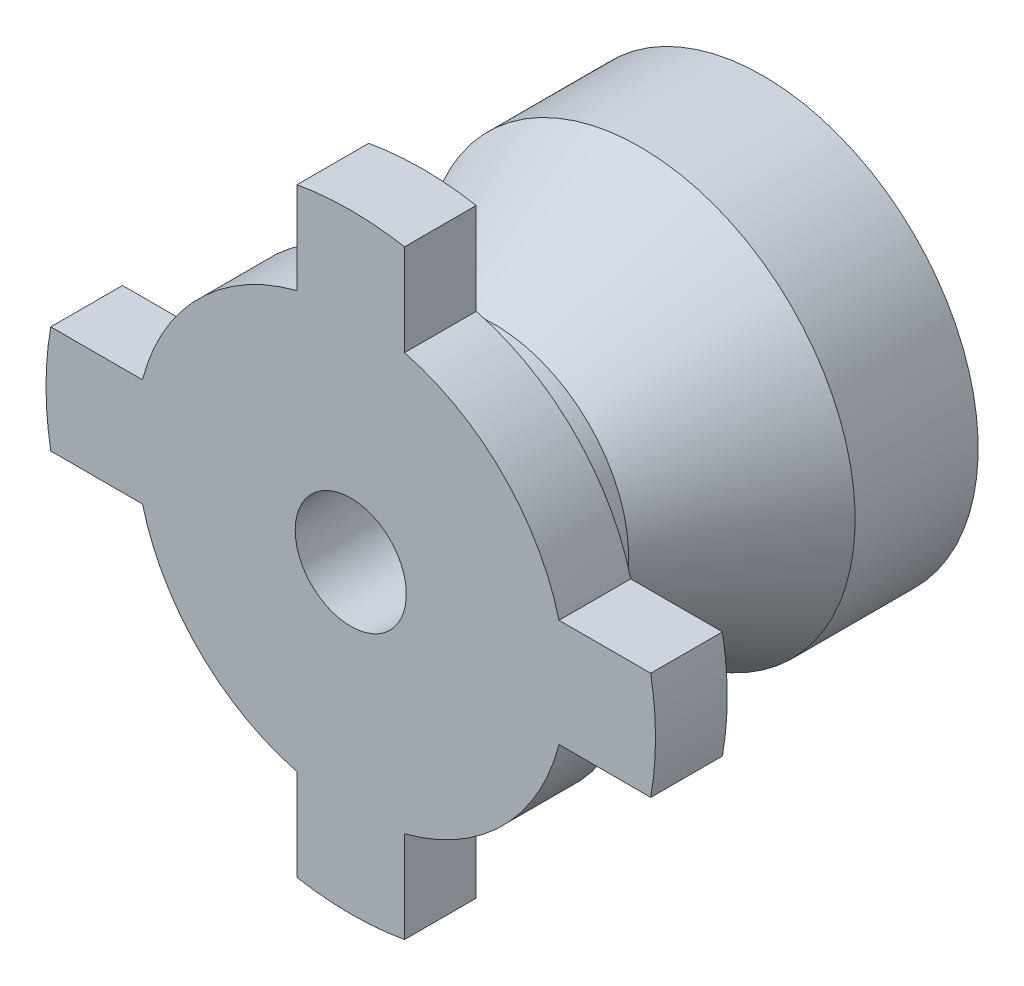
SolidWorks part; units mm, degrees
ref_plane "Front Plane" through (0, 0, 0) normal (0, 0, 1) x (1, 0, 0)
ref_plane "Top Plane" through (0, 0, 0) normal (0, 1, 0) x (1, 0, 0)
ref_plane "Right Plane" through (0, 0, 0) normal (1, 0, 0) x (0, 0, -1)
sketch "Sketch1" plane through (0, 0, 0) normal (0, 1, 0) x (1, 0, 0)
  line L0 (-20.9062, 0) -> (-6, 0) construction
  line L1 (0, 14.2603) -> (0, -16.1973) construction
  line L2 (-1.55, 0) -> (-6, 0)
  line L3 (0, 0) -> (23.1772, 0) construction
  line L4 (-6, 0) -> (-6, 2)
  line L5 (-6, 2) -> (-3.75, 2)
  line L6 (-3.75, 2) -> (-3.75, 4)
  line L7 (-3.75, 4) -> (-6, 8.0672)
  line L8 (-6, 8.0672) -> (-6, 11.5)
  line L9 (-6, 11.5) -> (-5, 11.5)
  line L10 (-5, 11.5) -> (-5, 9)
  line L11 (-5, 9) -> (-2.6884, 9)
  line L12 (-2.6884, 9) -> (-2.6884, 7.5)
  line L13 (-2.6884, 7.5) -> (-1.55, 7.5)
  line L14 (-1.55, 7.5) -> (-1.55, 0)
  point P7 (-1.55, 0)
  point P9 (-3.75, 0)
  point P10 (0, 11.5)
  dimension "D1" = 6
  dimension "D2" = 1.55
  dimension "D3" = 3.75
  dimension "D4" = 2
  dimension "D5" = 11.5
  dimension "D6" = 4
  dimension "D7" = 1.5
  dimension "D8" = 5
  dimension "D9" = 6
  dimension "D10" = 2.5
revolve "Revolve1" add sketch "Sketch1" angle 360 about L1
sketch "Sketch2" plane through (0, 0, 0) normal (0, 0, 1) x (1, 0, 0)
  line L0 (0, 9.4104) -> (0, -10.1354) construction
  line L1 (-13.1705, 0) -> (10.5119, 0) construction
  line L3 (-8.3666, 1.5) -> (-5.8095, 1.5)
  line L4 (-8.3666, -1.5) -> (-5.8095, -1.5)
  line L5 (1.5, 8.3666) -> (1.5, 5.8095)
  line L6 (-1.5, 8.3666) -> (-1.5, 5.8095)
  line L8 (8.3666, -1.5) -> (5.8095, -1.5)
  line L9 (8.3666, 1.5) -> (5.8095, 1.5)
  line L11 (-1.5, -8.3666) -> (-1.5, -5.8095)
  line L12 (1.5, -8.3666) -> (1.5, -5.8095)
  arc A0 (-5.8095, 1.5) -> (-5.8095, -1.5) centre (0, 0) ccw
  arc A1 (1.5, 5.8095) -> (-1.5, 5.8095) centre (0, 0) ccw
  arc A2 (5.8095, -1.5) -> (5.8095, 1.5) centre (0, 0) ccw
  arc A3 (-1.5, -5.8095) -> (1.5, -5.8095) centre (0, 0) ccw
  arc A4 (-8.3666, 1.5) -> (-8.3666, -1.5) centre (0, 0) ccw
  arc A5 (-1.5, -8.3666) -> (1.5, -8.3666) centre (0, 0) ccw
  arc A6 (8.3666, -1.5) -> (8.3666, 1.5) centre (0, 0) ccw
  arc A7 (1.5, 8.3666) -> (-1.5, 8.3666) centre (0, 0) ccw
  circle A8 centre (0, 0) radius 6 construction
  point P12 (0, 0)
  point P26 (0, 0)
  dimension "D4" = 17
  dimension "D1" = 3
  dimension "D2" = 1.5
  dimension "D3" = 4
extrude "Boss-Extrude1" add sketch "Sketch2" against normal blind 2
